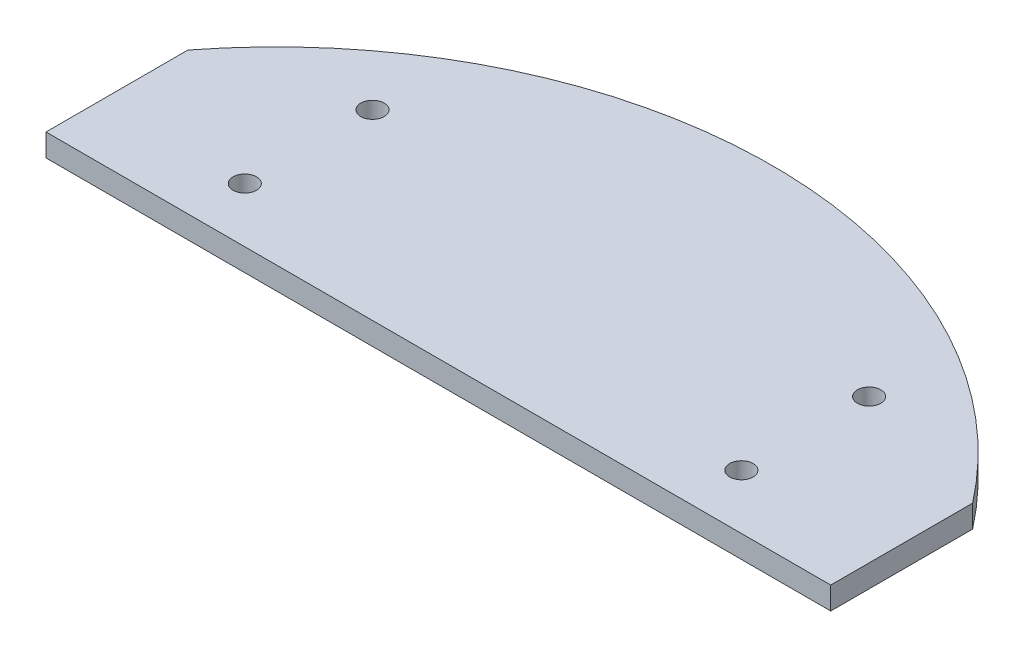
SolidWorks part; units mm, degrees
ref_plane "Front Plane" through (0, 0, 0) normal (0, 0, 1) x (1, 0, 0)
ref_plane "Top Plane" through (0, 0, 0) normal (0, 1, 0) x (1, 0, 0)
ref_plane "Right Plane" through (0, 0, 0) normal (1, 0, 0) x (0, 0, -1)
sketch "Sketch1" plane through (0, 0, 0) normal (0, 1, 0) x (1, 0, 0)
  line L0 (0, 70) -> (0, 22.9088) construction
  line L1 (35, 22.9088) -> (35, 60.6218) construction
  line L3 (0, 0) -> (49.4975, 49.4975) construction
  line L4 (0, 0) -> (26.7878, 64.6716) construction
  line L15 (0, 0) -> (-26.7878, 64.6716) construction
  line L16 (0, 0) -> (-49.4975, 49.4975) construction
  line L18 (-55.3067, 42.9088) -> (-55.3067, 22.9088)
  line L19 (55.3067, 42.9088) -> (55.3067, 22.9088)
  line L20 (-55.3067, 22.9088) -> (55.3067, 22.9088)
  arc A14 (55.3067, 42.9088) -> (-55.3067, 42.9088) centre (0, 0) ccw
  circle A15 centre (35, 48.6218) radius 1.65
  circle A16 centre (35, 30.6218) radius 1.65
  circle A17 centre (-35, 30.6218) radius 1.65
  circle A18 centre (-35, 48.6218) radius 1.65
  dimension "D1" = 35
  dimension "D5" = 3.3
  dimension "D9" = 20
  dimension "D2" = 12
  dimension "D3" = 18
  dimension "D4" = 22.5
extrude "Boss-Extrude2" add sketch "Sketch1" along normal blind 3.175
